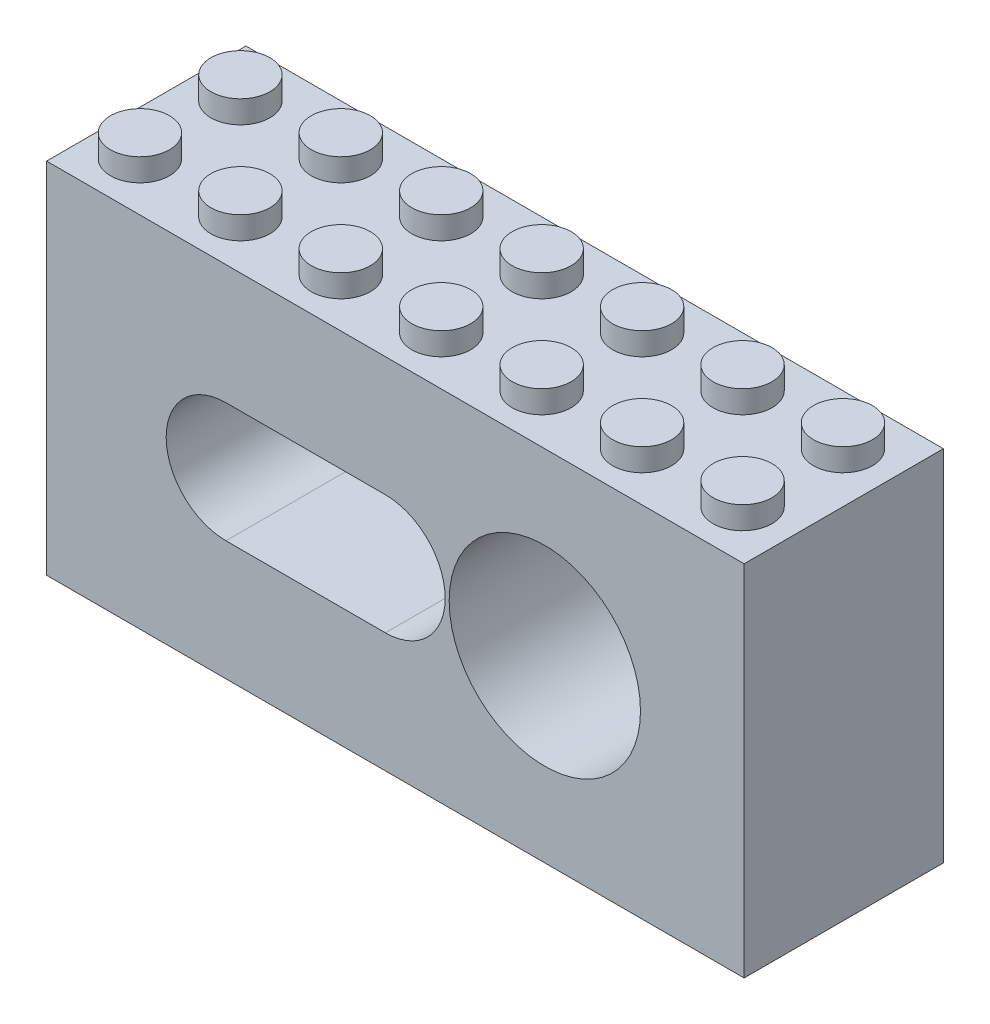
SolidWorks part; units mm, degrees
material "Custom Plastic"
ref_plane "Front Plane" through (0, 0, 0) normal (0, 0, 1) x (1, 0, 0)
ref_plane "Top Plane" through (0, 0, 0) normal (0, 1, 0) x (1, 0, 0)
ref_plane "Right Plane" through (0, 0, 0) normal (1, 0, 0) x (0, 0, -1)
sketch "Sketch1" plane through (0, 0, 0) normal (0, 1, 0) x (1, 0, 0)
  line L1 (-94.449, 51.0406) -> (-38.8865, 51.0406)
  line L2 (-94.449, 51.0406) -> (-94.449, 19.2906)
  line L3 (-94.449, 19.2906) -> (-38.8865, 19.2906)
  line L4 (-38.8865, 51.0406) -> (-38.8865, 19.2906)
  dimension "D1" = 55.5625
  dimension "D2" = 31.75
extrude "Boss-Extrude1" add sketch "Sketch1" along normal blind 28.575
sketch "Sketch2" plane through (0, 0, -19.2906) normal (0, 0, 1) x (1, 0, 0)
  line L0 (-94.449, 28.575) -> (-38.8865, 28.575) construction
  line L2 (-38.8865, 28.575) -> (-38.8865, 0) construction
  circle A0 centre (-54.7615, 14.2875) radius 7.62
  dimension "D3" = 15.24
  dimension "D1" = 14.2875
  dimension "D2" = 15.875
extrude "Cut-Extrude1" cut sketch "Sketch2" against normal blind 13.335
sketch "Sketch3" plane through (0, 0, -19.2906) normal (0, 0, 1) x (1, 0, 0)
  line L0 (-94.449, 28.575) -> (-38.8865, 28.575) construction
  line L1 (-94.449, 28.575) -> (-38.8865, 28.575)
  line L2 (-80.1615, 14.2875) -> (-67.4615, 14.2875) construction
  line L3 (-80.1615, 19.05) -> (-67.4615, 19.05)
  line L4 (-80.1615, 9.525) -> (-67.4615, 9.525)
  arc A0 (-80.1615, 19.05) -> (-80.1615, 9.525) centre (-80.1615, 14.2875) ccw
  circle A1 centre (-54.7615, 14.2875) radius 7.62
  circle A2 centre (-54.7615, 14.2875) radius 7.62
  arc A3 (-67.4615, 9.525) -> (-67.4615, 19.05) centre (-67.4615, 14.2875) ccw
  point P7 (-73.8115, 14.2875)
  dimension "D4" = 4.7625
  dimension "D2" = 12.7
  dimension "D3" = 12.7
  dimension "D1" = 0
extrude "Cut-Extrude2" cut sketch "Sketch3" against normal blind 12.7
sketch "Sketch4" plane through (0, 0, -31.9906) normal (0, 0, 1) x (1, 0, 0)
  line L2 (-80.1615, 9.525) -> (-67.4615, 9.525)
  line L3 (-67.4615, 19.05) -> (-80.1615, 19.05)
  line L4 (-80.1615, 9.525) -> (-67.4615, 9.525)
  line L5 (-67.4615, 19.05) -> (-80.1615, 19.05)
  arc A2 (-67.4615, 9.525) -> (-67.4615, 19.05) centre (-67.4615, 14.2875) ccw
  arc A3 (-80.1615, 19.05) -> (-80.1615, 9.525) centre (-80.1615, 14.2875) ccw
  arc A4 (-67.4615, 9.525) -> (-67.4615, 19.05) centre (-67.4615, 14.2875) ccw
  arc A5 (-80.1615, 19.05) -> (-80.1615, 9.525) centre (-80.1615, 14.2875) ccw
  circle A6 centre (-80.1615, 14.2875) radius 1.8415
  circle A7 centre (-67.4615, 14.2875) radius 1.8415
  dimension "D2" = 3.683
  dimension "D3" = 3.683
  dimension "D1" = 0
extrude "Cut-Extrude3" cut sketch "Sketch4" against normal blind 25.4 contours A7 | A6
sketch "Sketch5" plane through (0, 0, -51.0406) normal (0, 0, -1) x (-1, 0, 0)
  line L2 (67.4615, 9.525) -> (80.1615, 9.525)
  line L3 (80.1615, 19.05) -> (67.4615, 19.05)
  line L4 (38.8865, 0) -> (94.449, 0)
  line L5 (94.449, 0) -> (94.449, 28.575)
  line L6 (94.449, 28.575) -> (38.8865, 28.575)
  line L7 (38.8865, 28.575) -> (38.8865, 0)
  line L8 (38.8865, 0) -> (94.449, 0)
  line L9 (94.449, 0) -> (94.449, 28.575)
  line L10 (94.449, 28.575) -> (38.8865, 28.575)
  line L11 (38.8865, 28.575) -> (38.8865, 0)
  line L12 (67.4615, 9.525) -> (80.1615, 9.525)
  line L13 (80.1615, 19.05) -> (67.4615, 19.05)
  arc A2 (67.4615, 19.05) -> (67.4615, 9.525) centre (67.4615, 14.2875) ccw
  arc A3 (80.1615, 9.525) -> (80.1615, 19.05) centre (80.1615, 14.2875) ccw
  arc A4 (67.4615, 19.05) -> (67.4615, 9.525) centre (67.4615, 14.2875) ccw
  arc A5 (80.1615, 9.525) -> (80.1615, 19.05) centre (80.1615, 14.2875) ccw
  dimension "D1" = 0
  dimension "D2" = 0
extrude "Cut-Extrude4" cut sketch "Sketch5" against normal blind 17.78 contours L13 A4 L12 A5
sketch "Sketch6" plane through (0, 0, -51.0406) normal (0, 0, -1) x (-1, 0, 0)
  line L4 (38.8865, 0) -> (94.449, 0)
  line L5 (94.449, 0) -> (94.449, 28.575)
  line L6 (94.449, 28.575) -> (38.8865, 28.575)
  line L7 (38.8865, 28.575) -> (38.8865, 0)
  line L8 (38.8865, 0) -> (94.449, 0)
  line L9 (94.449, 0) -> (94.449, 28.575)
  line L10 (94.449, 28.575) -> (38.8865, 28.575)
  line L11 (38.8865, 28.575) -> (38.8865, 0)
  dimension "D1" = 0
extrude "Cut-Extrude5" cut sketch "Sketch6" against normal blind 15.875
sketch "Sketch7" plane through (0, 0, -32.6256) normal (0, 0, 1) x (1, 0, 0)
  circle A0 centre (-54.7615, 14.2875) radius 2.7781
  dimension "D2" = 5.5562
extrude "Cut-Extrude7" cut sketch "Sketch7" against normal blind 7.9375
sketch "Sketch8" plane through (0, 28.575, 0) normal (0, 1, 0) x (1, 0, 0)
  line L0 (-38.8865, 19.2906) -> (-38.8865, 35.1656) construction
  line L1 (-94.449, 35.1656) -> (-38.8865, 35.1656) construction
  circle A0 centre (-42.8865, 31.1656) radius 2.35
  circle A1 centre (-42.8865, 23.1656) radius 2.35
  circle A2 centre (-50.8865, 31.1656) radius 2.35
  circle A3 centre (-50.8865, 23.1656) radius 2.35
  circle A4 centre (-58.8865, 31.1656) radius 2.35
  circle A5 centre (-58.8865, 23.1656) radius 2.35
  circle A6 centre (-66.8865, 31.1656) radius 2.35
  circle A7 centre (-66.8865, 23.1656) radius 2.35
  circle A8 centre (-74.8865, 31.1656) radius 2.35
  circle A9 centre (-74.8865, 23.1656) radius 2.35
  circle A10 centre (-82.8865, 31.1656) radius 2.35
  circle A11 centre (-82.8865, 23.1656) radius 2.35
  circle A12 centre (-90.8865, 31.1656) radius 2.35
  circle A13 centre (-90.8865, 23.1656) radius 2.35
  dimension "D1" = 4.7
  dimension "D2" = 4.7
  dimension "D3" = 4
  dimension "D4" = 4
  dimension "D5" = 4
  dimension "D6" = 8
  dimension "D7" = 7
extrude "Boss-Extrude2" add sketch "Sketch8" along normal blind 1.8
sketch "Sketch9" plane through (0, 0, 0) normal (0, -1, 0) x (1, 0, 0)
  line L0 (-94.449, -19.2906) -> (-38.8865, -19.2906) construction
  line L1 (-38.8865, -19.2906) -> (-38.8865, -35.1656) construction
  line L2 (-82.875, -20.4906) -> (-82.875, -20.7906)
  line L3 (-94.449, -19.2906) -> (-38.8865, -19.2906)
  line L4 (-94.449, -19.2906) -> (-94.449, -35.1656)
  line L5 (-94.449, -35.1656) -> (-38.8865, -35.1656)
  line L6 (-38.8865, -19.2906) -> (-38.8865, -35.1656)
  line L7 (-40.0865, -33.9656) -> (-93.249, -33.9656)
  line L8 (-40.0865, -33.9656) -> (-40.0865, -20.4906)
  line L9 (-40.0865, -20.4906) -> (-93.249, -20.4906)
  line L10 (-93.249, -33.9656) -> (-93.249, -20.4906)
  line L11 (-93.249, -22.9906) -> (-92.949, -22.9906)
  line L12 (-93.249, -22.9906) -> (-93.249, -23.5906)
  line L13 (-93.249, -23.5906) -> (-92.949, -23.5906)
  line L14 (-92.949, -22.9906) -> (-92.949, -23.5906)
  line L15 (-90.749, -20.4906) -> (-90.149, -20.4906)
  line L16 (-90.749, -20.4906) -> (-90.749, -20.7906)
  line L17 (-90.749, -20.7906) -> (-90.149, -20.7906)
  line L18 (-90.149, -20.4906) -> (-90.149, -20.7906)
  line L19 (-90.749, -33.9656) -> (-90.149, -33.9656)
  line L20 (-90.749, -33.9656) -> (-90.749, -33.6656)
  line L21 (-90.749, -33.6656) -> (-90.149, -33.6656)
  line L22 (-90.149, -33.9656) -> (-90.149, -33.6656)
  line L23 (-82.875, -20.7906) -> (-82.275, -20.7906)
  line L24 (-82.275, -20.4906) -> (-82.275, -20.7906)
  line L25 (-82.875, -33.9656) -> (-82.875, -33.6656)
  line L26 (-82.875, -33.6656) -> (-82.275, -33.6656)
  line L27 (-82.275, -33.9656) -> (-82.275, -33.6656)
  line L28 (-75.001, -20.4906) -> (-75.001, -20.7906)
  line L29 (-75.001, -20.7906) -> (-74.401, -20.7906)
  line L30 (-74.401, -20.4906) -> (-74.401, -20.7906)
  line L31 (-75.001, -33.9656) -> (-75.001, -33.6656)
  line L32 (-75.001, -33.6656) -> (-74.401, -33.6656)
  line L33 (-74.401, -33.9656) -> (-74.401, -33.6656)
  line L34 (-67.127, -20.4906) -> (-67.127, -20.7906)
  line L35 (-67.127, -20.7906) -> (-66.527, -20.7906)
  line L36 (-66.527, -20.4906) -> (-66.527, -20.7906)
  line L37 (-67.127, -33.9656) -> (-67.127, -33.6656)
  line L38 (-67.127, -33.6656) -> (-66.527, -33.6656)
  line L39 (-66.527, -33.9656) -> (-66.527, -33.6656)
  line L40 (-59.253, -20.4906) -> (-59.253, -20.7906)
  line L41 (-59.253, -20.7906) -> (-58.653, -20.7906)
  line L42 (-58.653, -20.4906) -> (-58.653, -20.7906)
  line L43 (-59.253, -33.9656) -> (-59.253, -33.6656)
  line L44 (-59.253, -33.6656) -> (-58.653, -33.6656)
  line L45 (-58.653, -33.9656) -> (-58.653, -33.6656)
  line L46 (-51.379, -20.4906) -> (-51.379, -20.7906)
  line L47 (-51.379, -20.7906) -> (-50.779, -20.7906)
  line L48 (-50.779, -20.4906) -> (-50.779, -20.7906)
  line L49 (-51.379, -33.9656) -> (-51.379, -33.6656)
  line L50 (-51.379, -33.6656) -> (-50.779, -33.6656)
  line L51 (-50.779, -33.9656) -> (-50.779, -33.6656)
  line L52 (-43.505, -20.4906) -> (-43.505, -20.7906)
  line L53 (-43.505, -20.7906) -> (-42.905, -20.7906)
  line L54 (-42.905, -20.4906) -> (-42.905, -20.7906)
  line L55 (-43.505, -33.9656) -> (-43.505, -33.6656)
  line L56 (-43.505, -33.6656) -> (-42.905, -33.6656)
  line L57 (-42.905, -33.9656) -> (-42.905, -33.6656)
  line L58 (-93.249, -30.9906) -> (-92.949, -30.9906)
  line L59 (-92.949, -30.9906) -> (-92.949, -31.5906)
  line L60 (-93.249, -31.5906) -> (-92.949, -31.5906)
  circle A0 centre (-46.8865, -27.2906) radius 3.25
  circle A1 centre (-46.8865, -27.2906) radius 2.425
  circle A2 centre (-54.8865, -27.2906) radius 3.25
  circle A3 centre (-54.8865, -27.2906) radius 2.425
  circle A4 centre (-62.8865, -27.2906) radius 3.25
  circle A5 centre (-62.8865, -27.2906) radius 2.425
  circle A6 centre (-70.8865, -27.2906) radius 3.25
  circle A7 centre (-70.8865, -27.2906) radius 2.425
  circle A8 centre (-78.8865, -27.2906) radius 3.25
  circle A9 centre (-78.8865, -27.2906) radius 2.425
  circle A10 centre (-86.8865, -27.2906) radius 3.25
  circle A11 centre (-86.8865, -27.2906) radius 2.425
  dimension "D3" = 6.5
  dimension "D4" = 4.85
  dimension "D1" = 8
  dimension "D2" = 8
  dimension "D6" = 1.2
  dimension "D7" = 1.2
  dimension "D8" = 1.2
  dimension "D9" = 1.2
  dimension "D10" = 0.6
  dimension "D11" = 0.6
  dimension "D12" = 0.3
  dimension "D13" = 0.3
  dimension "D14" = 0.3
  dimension "D15" = 0.6
  dimension "D16" = 3.7
  dimension "D17" = 3.7
  dimension "D19" = 3.7
  dimension "D5" = 6
  dimension "D18" = 7
  dimension "D20" = 2
extrude "Cut-Extrude8" cut sketch "Sketch9" against normal blind 2.1 contours L60 L10 L7 L20 L21 L22 L25 L26 L27 L31 L32 L33 L37 L38 L39 L43 L44 L45 L49 L50 L51 L55 L56 L57 L8 L9 L54 L53 L52 L48 L47 L46 L42 L41 L40 L36 L35 L34 L30 L29 | A11 | A9 | A7 | A5 | A3 | A1
